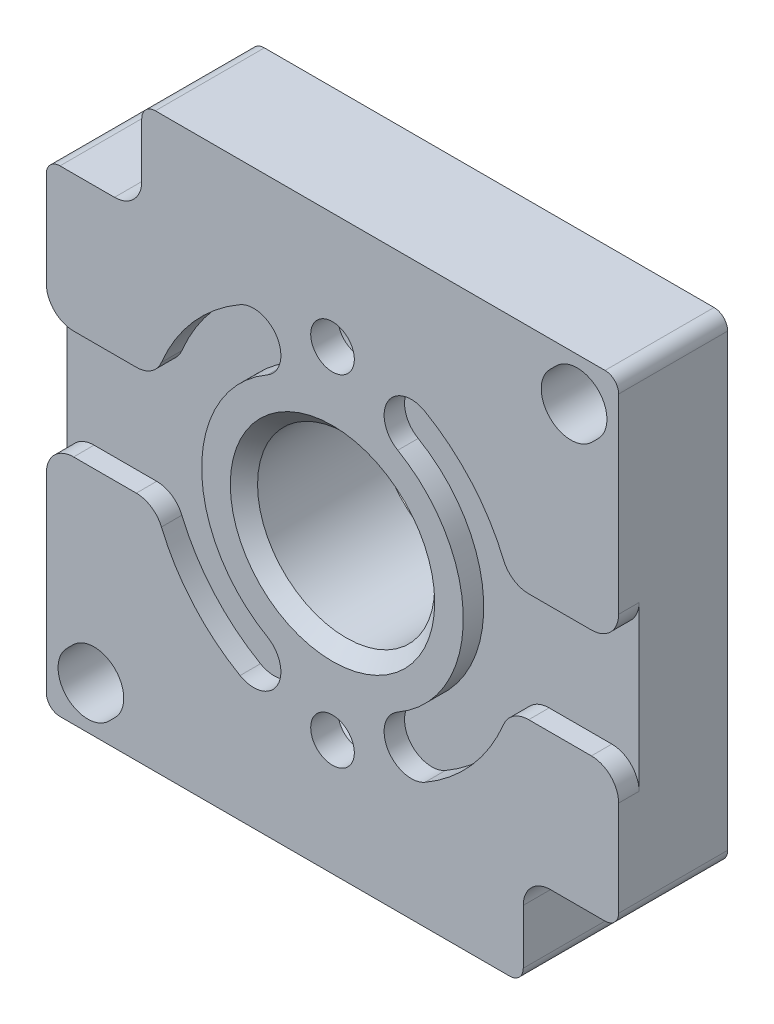
SolidWorks part; units mm, degrees
ref_plane "Front Plane" through (0, 0, 0) normal (0, 0, 1) x (1, 0, 0)
ref_plane "Top Plane" through (0, 0, 0) normal (0, 1, 0) x (1, 0, 0)
ref_plane "Right Plane" through (0, 0, 0) normal (1, 0, 0) x (0, 0, -1)
ref_plane "Plane1" through (0, 0, -7) normal (0, 0, -1) x (-1, 0, 0)
sketch "Sketch1" plane through (0, 0, -7) normal (0, 0, -1) x (-1, 0, 0)
  line L0 (21, -21) -> (21, 21)
  line L1 (21, 21) -> (-21, 21)
  line L2 (-21, 21) -> (-21, -21)
  line L3 (-21, -21) -> (21, -21)
extrude "Boss-Extrude1" add sketch "Sketch1" against normal blind 8
sketch "Sketch2" plane through (0, 0, -7) normal (0, 0, -1) x (-1, 0, 0)
  arc A0 (3.1982, -13.078) -> (-3.1982, -13.078) centre (0, -12.5) ccw
  arc A1 (-3.1982, -13.078) -> (-4.4831, -14.2096) centre (-4.1822, -13.2559) cw
  arc A2 (-4.4831, -14.2096) -> (-4.4831, 14.2096) centre (0, 0) cw
  arc A3 (-4.4831, 14.2096) -> (-3.1982, 13.078) centre (-4.1822, 13.2559) cw
  arc A4 (-3.1982, 13.078) -> (3.1982, 13.078) centre (0, 12.5) ccw
  arc A5 (3.1982, 13.078) -> (4.4831, 14.2096) centre (4.1822, 13.2559) cw
  arc A6 (4.4831, 14.2096) -> (4.4831, -14.2096) centre (0, 0) cw
  arc A7 (4.4831, -14.2096) -> (3.1982, -13.078) centre (4.1822, -13.2559) cw
extrude "Boss-Extrude2" add sketch "Sketch2" along normal blind 1.8
sketch "Sketch3" plane through (0, 0, -7) normal (0, 0, -1) x (-1, 0, 0)
  line L0 (13.5667, 6.1607) -> (19, 8.4113)
  line L1 (19, 8.4113) -> (19, 12)
  line L2 (19, 12) -> (12, 12)
  line L3 (12, 12) -> (12, 19)
  line L4 (12, 19) -> (-13.5984, 19)
  line L5 (-19, 13.5984) -> (-19, 8.4113)
  line L6 (-19, 8.4113) -> (-13.5667, 6.1607)
  arc A0 (-4.4831, 14.2096) -> (-3.1982, 13.078) centre (-4.1822, 13.2559) cw
  arc A1 (-3.1982, 13.078) -> (3.1982, 13.078) centre (0, 12.5) ccw
  arc A2 (3.1982, 13.078) -> (4.4831, 14.2096) centre (4.1822, 13.2559) cw
  arc A3 (4.4831, 14.2096) -> (13.5667, 6.1607) centre (0, 0) cw
  arc A4 (-13.5984, 19) -> (-19, 13.5984) centre (-17.5, 17.5) cw
  arc A5 (-13.5667, 6.1607) -> (-4.4831, 14.2096) centre (0, 0) cw
extrude "Cut-Extrude1" cut sketch "Sketch3" against normal blind 6
sketch "Sketch4" plane through (0, 0, -7) normal (0, 0, -1) x (-1, 0, 0)
  line L0 (-13.9494, 5.2368) -> (-19, 7.3289)
  line L1 (-19, 7.3289) -> (-19, -7.3289)
  line L2 (-19, -7.3289) -> (-13.9494, -5.2368)
  arc A0 (-13.9494, -5.2368) -> (-13.9494, 5.2368) centre (0, 0) cw
extrude "Cut-Extrude2" cut sketch "Sketch4" against normal blind 6
sketch "Sketch5" plane through (0, 0, -7) normal (0, 0, -1) x (-1, 0, 0)
  line L0 (-13.5667, -6.1607) -> (-19, -8.4113)
  line L1 (-19, -8.4113) -> (-19, -12)
  line L2 (-19, -12) -> (-12, -12)
  line L3 (-12, -12) -> (-12, -19)
  line L4 (-12, -19) -> (13.5984, -19)
  line L5 (19, -13.5984) -> (19, -8.4113)
  line L6 (19, -8.4113) -> (13.5667, -6.1607)
  arc A0 (13.5984, -19) -> (19, -13.5984) centre (17.5, -17.5) cw
  arc A1 (13.5667, -6.1607) -> (4.4831, -14.2096) centre (0, 0) cw
  arc A2 (4.4831, -14.2096) -> (3.1982, -13.078) centre (4.1822, -13.2559) cw
  arc A3 (3.1982, -13.078) -> (-3.1982, -13.078) centre (0, -12.5) ccw
  arc A4 (-3.1982, -13.078) -> (-4.4831, -14.2096) centre (-4.1822, -13.2559) cw
  arc A5 (-4.4831, -14.2096) -> (-13.5667, -6.1607) centre (0, 0) cw
extrude "Cut-Extrude3" cut sketch "Sketch5" against normal blind 6
sketch "Sketch6" plane through (0, 0, -7) normal (0, 0, -1) x (-1, 0, 0)
  line L0 (13.9494, -5.2368) -> (19, -7.3289)
  line L1 (19, -7.3289) -> (19, 7.3289)
  line L2 (19, 7.3289) -> (13.9494, 5.2368)
  arc A0 (13.9494, 5.2368) -> (13.9494, -5.2368) centre (0, 0) cw
extrude "Cut-Extrude4" cut sketch "Sketch6" against normal blind 6
sketch "Sketch7" plane through (0, 0, 1) normal (0, 0, 1) x (1, 0, 0)
  line L0 (21, 4) -> (12.9985, 4)
  line L1 (12.9985, -4) -> (21, -4)
  line L2 (21, -4) -> (21, 4)
  arc A0 (12.9985, 4) -> (6.7852, 11.7865) centre (0, 0) ccw
  arc A1 (6.7852, 11.7865) -> (4.7896, 8.3199) centre (5.7874, 10.0532) ccw
  arc A2 (4.7896, 8.3199) -> (4.7896, -8.3199) centre (0, 0) cw
  arc A3 (4.7896, -8.3199) -> (6.7852, -11.7865) centre (5.7874, -10.0532) ccw
  arc A4 (6.7852, -11.7865) -> (12.9985, -4) centre (0, 0) ccw
extrude "Cut-Extrude5" cut sketch "Sketch7" against normal blind 1.5
sketch "Sketch8" plane through (0, 0, 1) normal (0, 0, 1) x (1, 0, 0)
  line L0 (-21, -4) -> (-12.9985, -4)
  line L1 (-12.9985, 4) -> (-21, 4)
  line L2 (-21, 4) -> (-21, -4)
  arc A0 (-12.9985, -4) -> (-6.7852, -11.7865) centre (0, 0) ccw
  arc A1 (-6.7852, -11.7865) -> (-4.7896, -8.3199) centre (-5.7874, -10.0532) ccw
  arc A2 (-4.7896, -8.3199) -> (-4.7896, 8.3199) centre (0, 0) cw
  arc A3 (-4.7896, 8.3199) -> (-6.7852, 11.7865) centre (-5.7874, 10.0532) ccw
  arc A4 (-6.7852, 11.7865) -> (-12.9985, 4) centre (0, 0) ccw
extrude "Cut-Extrude6" cut sketch "Sketch8" against normal blind 1.5
sketch "Sketch9" plane through (0, 0, 1) normal (0, 0, 1) x (1, 0, 0)
  line L0 (-21, 14) -> (-14, 14)
  line L1 (-14, 14) -> (-14, 21)
  line L2 (-14, 21) -> (-21, 21)
  line L3 (-21, 21) -> (-21, 14)
extrude "Cut-Extrude7" cut sketch "Sketch9" against normal through all
sketch "Sketch10" plane through (0, 0, 1) normal (0, 0, 1) x (1, 0, 0)
  line L0 (21, -14) -> (14, -14)
  line L1 (14, -14) -> (14, -21)
  line L2 (14, -21) -> (21, -21)
  line L3 (21, -21) -> (21, -14)
extrude "Cut-Extrude8" cut sketch "Sketch10" against normal through all
sketch "Sketch11" plane through (0, 0, -7) normal (0, 0, -1) x (-1, 0, 0)
  line L0 (-15.9585, 19.0415) -> (-16.419, 19.502)
  line L1 (-19.502, 16.419) -> (-19.0415, 15.9585)
  arc A0 (-19.0415, 15.9585) -> (-15.9585, 19.0415) centre (-17.5, 17.5) ccw
  arc A1 (-16.419, 19.502) -> (-19.502, 16.419) centre (-17.9605, 17.9605) ccw
extrude "Cut-Extrude9" cut sketch "Sketch11" against normal through all
sketch "Sketch12" plane through (0, 0, 1) normal (0, 0, 1) x (1, 0, 0)
  line L0 (-16.419, -19.502) -> (-15.9585, -19.0415)
  line L1 (-19.0415, -15.9585) -> (-19.502, -16.419)
  arc A0 (-19.502, -16.419) -> (-16.419, -19.502) centre (-17.9605, -17.9605) ccw
  arc A1 (-15.9585, -19.0415) -> (-19.0415, -15.9585) centre (-17.5, -17.5) ccw
extrude "Cut-Extrude10" cut sketch "Sketch12" against normal through all
sketch "Sketch13" plane through (0, 0, -8.8) normal (0, 0, -1) x (-1, 0, 0)
  line L0 (12.18, -5.5863) -> (7.648, -3.7091)
  arc A0 (3.7281, -7.6388) -> (3.442, -9.2266) centre (4.1667, -8.5375) ccw
  arc A1 (3.442, -9.2266) -> (4.7499, -12.5299) centre (0, -12.5) cw
  arc A2 (4.7499, -12.5299) -> (12.18, -5.5863) centre (0, 0) ccw
  arc A3 (7.648, -3.7091) -> (3.7281, -7.6388) centre (0, 0) cw
extrude "Cut-Extrude11" cut sketch "Sketch13" against normal blind 7.8
sketch "Sketch14" plane through (0, 0, -8.8) normal (0, 0, -1) x (-1, 0, 0)
  line L0 (-12.18, 5.5863) -> (-7.648, 3.7091)
  arc A0 (-3.7281, 7.6388) -> (-3.442, 9.2266) centre (-4.1667, 8.5375) ccw
  arc A1 (-3.442, 9.2266) -> (-4.7499, 12.5299) centre (0, 12.5) cw
  arc A2 (-4.7499, 12.5299) -> (-12.18, 5.5863) centre (0, 0) ccw
  arc A3 (-7.648, 3.7091) -> (-3.7281, 7.6388) centre (0, 0) cw
extrude "Cut-Extrude12" cut sketch "Sketch14" against normal blind 7.8
sketch "Sketch15" plane through (0, 0, -8.8) normal (0, 0, -1) x (-1, 0, 0)
  line L0 (7.648, 3.7091) -> (12.18, 5.5863)
  arc A0 (3.442, 9.2266) -> (3.7281, 7.6388) centre (4.1667, 8.5375) ccw
  arc A1 (3.7281, 7.6388) -> (7.648, 3.7091) centre (0, 0) cw
  arc A2 (12.18, 5.5863) -> (4.7499, 12.5299) centre (0, 0) ccw
  arc A3 (4.7499, 12.5299) -> (3.442, 9.2266) centre (0, 12.5) cw
extrude "Cut-Extrude13" cut sketch "Sketch15" against normal blind 7.8
sketch "Sketch16" plane through (0, 0, -8.8) normal (0, 0, -1) x (-1, 0, 0)
  line L0 (-7.648, -3.7091) -> (-12.18, -5.5863)
  arc A0 (-3.442, -9.2266) -> (-3.7281, -7.6388) centre (-4.1667, -8.5375) ccw
  arc A1 (-3.7281, -7.6388) -> (-7.648, -3.7091) centre (0, 0) cw
  arc A2 (-12.18, -5.5863) -> (-4.7499, -12.5299) centre (0, 0) ccw
  arc A3 (-4.7499, -12.5299) -> (-3.442, -9.2266) centre (0, -12.5) cw
extrude "Cut-Extrude14" cut sketch "Sketch16" against normal blind 7.8
sketch "Sketch17" plane through (0, 0, -8.8) normal (0, 0, -1) x (-1, 0, 0)
  line L0 (-12.5627, -4.6624) -> (-8.0307, -2.7852)
  line L1 (-8.0307, 2.7852) -> (-12.5627, 4.6624)
  arc A0 (-12.5627, 4.6624) -> (-12.5627, -4.6624) centre (0, 0) ccw
  arc A1 (-8.0307, -2.7852) -> (-8.0307, 2.7852) centre (0, 0) cw
extrude "Cut-Extrude15" cut sketch "Sketch17" against normal blind 7.8
sketch "Sketch18" plane through (0, 0, -8.8) normal (0, 0, -1) x (-1, 0, 0)
  line L0 (8.0307, -2.7852) -> (12.5627, -4.6624)
  line L1 (12.5627, 4.6624) -> (8.0307, 2.7852)
  arc A0 (12.5627, -4.6624) -> (12.5627, 4.6624) centre (0, 0) ccw
  arc A1 (8.0307, 2.7852) -> (8.0307, -2.7852) centre (0, 0) cw
extrude "Cut-Extrude16" cut sketch "Sketch18" against normal blind 7.8
hole_wizard "Ø3.2 (3.2) Diameter Hole1" positions "Sketch20" profile "Sketch19" hole size "Ø3.2" standard "ANSI Metric"
sketch "Sketch20" plane through (0, 0, -1) normal (0, 0, -1) x (-1, 0, 0)
  point P0 (0, -12.5)
  point P1 (0, 12.5)
sketch "Sketch19" plane through (0, -12.5, -1) normal (1, 0, 0) x (0, 1, 0)
  line L0 (0, 0) -> (0, 2)
  line L1 (0, 2) -> (1.6, 2)
  line L2 (1.6, 2) -> (1.6, 0)
  line L5 (1.6, 0) -> (0, 0)
  line L11 (0, -6.35) -> (0, 107.95) construction
  dimension "Thru Hole Dia." = 3.2
  dimension "Thru Hole Depth" = 2
hole_wizard "Ø13.0 (13) Diameter Hole1" positions "Sketch22" profile "Sketch21" hole size "Ø13.0" standard "ANSI Metric"
sketch "Sketch22" plane through (0, 0, 1) normal (0, 0, 1) x (1, 0, 0)
  point P0 (0, 0)
sketch "Sketch21" plane through (0, 0, 1) normal (1, 0, 0) x (0, -1, 0)
  line L0 (0, 0) -> (0, 9.8)
  line L1 (0, 9.8) -> (6.5, 9.8)
  line L2 (6.5, 9.8) -> (6.5, 0)
  line L5 (6.5, 0) -> (0, 0)
  line L11 (0, -6.35) -> (0, 107.95) construction
  dimension "Thru Hole Dia." = 13
  dimension "Thru Hole Depth" = 9.8
chamfer "Chamfer1" distance 1 angle 45 1 edges at (6.5, 0, 1)
chamfer "Chamfer2" distance 0.5 angle 45 8 edges at (3.5214, 14.0064, -8.8) (0, 9.25, -8.8) (14.9, 0, -8.8) (-3.5214, 14.0064, -8.8) (3.5214, -14.0064, -8.8) (-14.9, 0, -8.8) (0, -9.25, -8.8) (-3.5214, -14.0064, -8.8)
fillet "Fillet1" radius 1 26 edges at (14, -21, -3) (12.18, -5.5863, -4.9) (8.0307, 2.7852, -4.9) (-12.5627, -4.6624, -4.9) (-21, 14, -3) (-8.0307, -2.7852, -4.9) (12.5627, -4.6624, -4.9) (-12.5627, 4.6624, -4.9) (-12.18, 5.5863, -4.9) (-4.7499, -12.5299, -4.9) (-14, 21, -3) (-7.648, -3.7091, -4.9) (-21, -21, -3) (-12.18, -5.5863, -4.9) (8.0307, -2.7852, -4.9) (4.7499, -12.5299, -4.9) (12.5627, 4.6624, -4.9) (7.648, 3.7091, -4.9) (-7.648, 3.7091, -4.9) (12.18, 5.5863, -4.9) (7.648, -3.7091, -4.9) (21, -14, -3) (21, 21, -3) (4.7499, 12.5299, -4.9) (-4.7499, 12.5299, -4.9) (-8.0307, 2.7852, -4.9)
fillet "Fillet2" radius 2 10 edges at (-14, 14, -3) (12.9985, 4, 0.25) (12.9985, -4, 0.25) (-12.9985, -4, 0.25) (21, 4, 0.25) (-21, 4, 0.25) (14, -14, -3) (-12.9985, 4, 0.25) (21, -4, 0.25) (-21, -4, 0.25)
fillet "Fillet3" radius 4 2 edges at (12, -12, -4) (-12, 12, -4)
